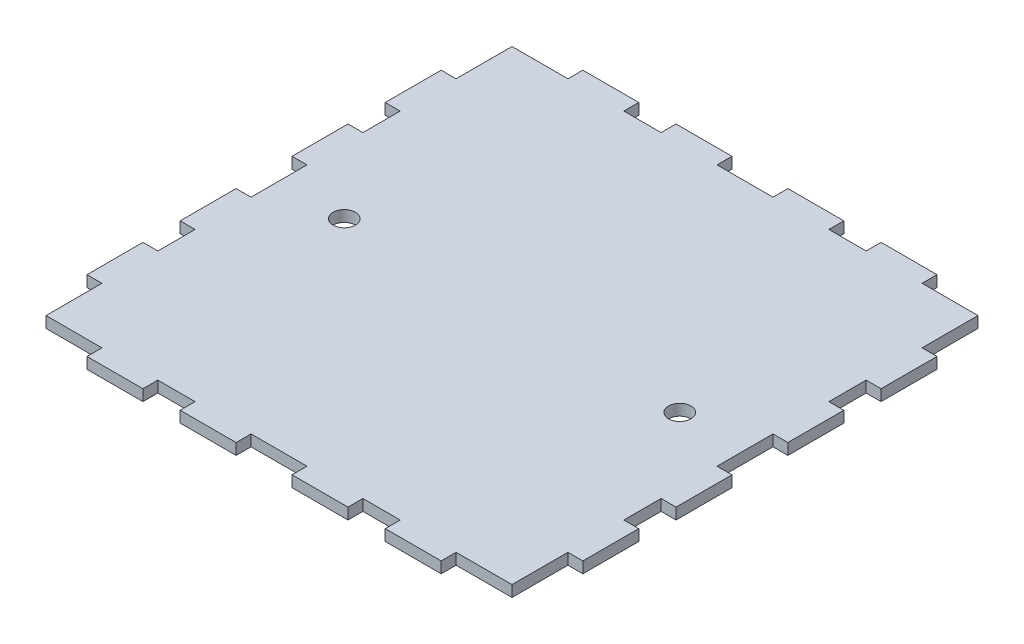
SolidWorks part; units mm, degrees
material "Oak"
ref_plane "Front Plane" through (0, 0, 0) normal (0, 0, 1) x (1, 0, 0)
ref_plane "Top Plane" through (0, 0, 0) normal (0, 1, 0) x (1, 0, 0)
ref_plane "Right Plane" through (0, 0, 0) normal (1, 0, 0) x (0, 0, -1)
sketch "Sketch1" plane through (0, 0, 0) normal (0, 1, 0) x (1, 0, 0)
  line L0 (-1.5, 0) -> (-62.5, 0) construction
  line L6 (7.5, -66.5) -> (7.5, -62.5)
  line L11 (-7.5, -62.5) -> (7.5, -62.5)
  line L12 (-7.5, -66.5) -> (-7.5, -62.5)
  line L14 (7.5, -66.5) -> (22.5, -66.5)
  line L15 (62.5, -59) -> (62.5, -62.5)
  line L31 (57.5, -62.5) -> (47.5, -62.5)
  line L32 (47.5, -62.5) -> (47.5, -66.5)
  line L33 (32.5, -62.5) -> (22.5, -62.5)
  line L34 (22.5, -62.5) -> (22.5, -66.5)
  line L35 (-22.5, -62.5) -> (-22.5, -66.5)
  line L36 (-32.5, -62.5) -> (-22.5, -62.5)
  line L37 (-32.5, -62.5) -> (-32.5, -66.5)
  line L39 (-47.5, -62.5) -> (-47.5, -66.5)
  line L40 (-59, -62.5) -> (-47.5, -62.5)
  line L41 (-22.5, -66.5) -> (-7.5, -66.5)
  line L42 (-47.5, -66.5) -> (-32.5, -66.5)
  line L44 (32.5, -62.5) -> (32.5, -66.5)
  line L45 (32.5, -66.5) -> (47.5, -66.5)
  line L61 (62.5, -47.5) -> (62.5, -59)
  line L62 (66.5, -47.5) -> (62.5, -47.5)
  line L63 (62.5, -22.5) -> (62.5, -32.5)
  line L64 (62.5, -32.5) -> (66.5, -32.5)
  line L65 (66.5, -22.5) -> (62.5, -22.5)
  line L69 (-62.5, -47.5) -> (-62.5, -59)
  line L70 (-66.5, -47.5) -> (-62.5, -47.5)
  line L71 (-62.5, -32.5) -> (-66.5, -32.5)
  line L72 (-62.5, -22.5) -> (-62.5, -32.5)
  line L73 (-66.5, -22.5) -> (-62.5, -22.5)
  line L85 (66.5, -32.5) -> (66.5, -47.5)
  line L87 (62.5, -62.5) -> (57.5, -62.5)
  line L92 (-62.5, -59) -> (-62.5, -62.5)
  line L93 (-62.5, -62.5) -> (-59, -62.5)
  line L96 (-66.5, -32.5) -> (-66.5, -47.5)
  line L101 (66.5, -22.5) -> (66.5, -7.5)
  line L102 (-66.5, -22.5) -> (-66.5, -7.5)
  line L103 (66.5, -7.5) -> (62.5, -7.5)
  line L104 (62.5, -7.5) -> (62.5, 7.5)
  line L105 (-66.5, -7.5) -> (-62.5, -7.5)
  line L106 (-62.5, -7.5) -> (-62.5, 7.5)
  line L107 (-66.5, 7.5) -> (-62.5, 7.5)
  line L108 (66.5, 7.5) -> (62.5, 7.5)
  line L109 (-66.5, 22.5) -> (-66.5, 7.5)
  line L110 (66.5, 22.5) -> (66.5, 7.5)
  line L111 (-66.5, 32.5) -> (-66.5, 47.5)
  line L112 (-62.5, 62.5) -> (-59, 62.5)
  line L113 (-62.5, 59) -> (-62.5, 62.5)
  line L114 (62.5, 62.5) -> (57.5, 62.5)
  line L115 (66.5, 32.5) -> (66.5, 47.5)
  line L116 (-66.5, 22.5) -> (-62.5, 22.5)
  line L117 (-62.5, 22.5) -> (-62.5, 32.5)
  line L118 (-62.5, 32.5) -> (-66.5, 32.5)
  line L119 (-66.5, 47.5) -> (-62.5, 47.5)
  line L120 (-62.5, 47.5) -> (-62.5, 59)
  line L121 (66.5, 22.5) -> (62.5, 22.5)
  line L122 (62.5, 32.5) -> (66.5, 32.5)
  line L123 (62.5, 22.5) -> (62.5, 32.5)
  line L124 (66.5, 47.5) -> (62.5, 47.5)
  line L125 (62.5, 47.5) -> (62.5, 59)
  line L126 (32.5, 66.5) -> (47.5, 66.5)
  line L127 (32.5, 62.5) -> (32.5, 66.5)
  line L128 (-47.5, 66.5) -> (-32.5, 66.5)
  line L129 (-22.5, 66.5) -> (-7.5, 66.5)
  line L130 (-59, 62.5) -> (-47.5, 62.5)
  line L131 (-47.5, 62.5) -> (-47.5, 66.5)
  line L132 (-32.5, 62.5) -> (-32.5, 66.5)
  line L133 (-32.5, 62.5) -> (-22.5, 62.5)
  line L134 (-22.5, 62.5) -> (-22.5, 66.5)
  line L135 (22.5, 62.5) -> (22.5, 66.5)
  line L136 (32.5, 62.5) -> (22.5, 62.5)
  line L137 (47.5, 62.5) -> (47.5, 66.5)
  line L138 (57.5, 62.5) -> (47.5, 62.5)
  line L139 (62.5, 59) -> (62.5, 62.5)
  line L140 (7.5, 66.5) -> (22.5, 66.5)
  line L141 (-7.5, 66.5) -> (-7.5, 62.5)
  line L142 (-7.5, 62.5) -> (7.5, 62.5)
  line L143 (7.5, 66.5) -> (7.5, 62.5)
  point P11 (-47.5, -64.5)
  point P12 (-62.5, 0)
  point P18 (62.5, 0)
  dimension "D4" = 10
  dimension "D5" = 15
  dimension "D6" = 15
  dimension "D7" = 15
  dimension "D8" = 15
  dimension "D9" = 15
  dimension "D10" = 15
  dimension "D11" = 15
  dimension "D12" = 62.5
  dimension "D13" = 10
  dimension "D14" = 7.5
  dimension "D15" = 62.5
  dimension "D16" = 62.5
  dimension "D17" = 15
  dimension "D26" = 15
  dimension "D27" = 15
  dimension "D28" = 15
  dimension "D30" = 10
extrude "Boss-Extrude1" add sketch "Sketch1" along normal blind 3
sketch "Sketch4" plane through (0, 0, 0) normal (0, 1, 0) x (1, 0, 0)
  line L0 (-58.4491, 0) -> (51.4693, 0) construction
  circle A1 centre (-45, 0) radius 3
  circle A2 centre (45, 0) radius 3
extrude "Cut-Extrude2" cut sketch "Sketch4" along normal blind 16
